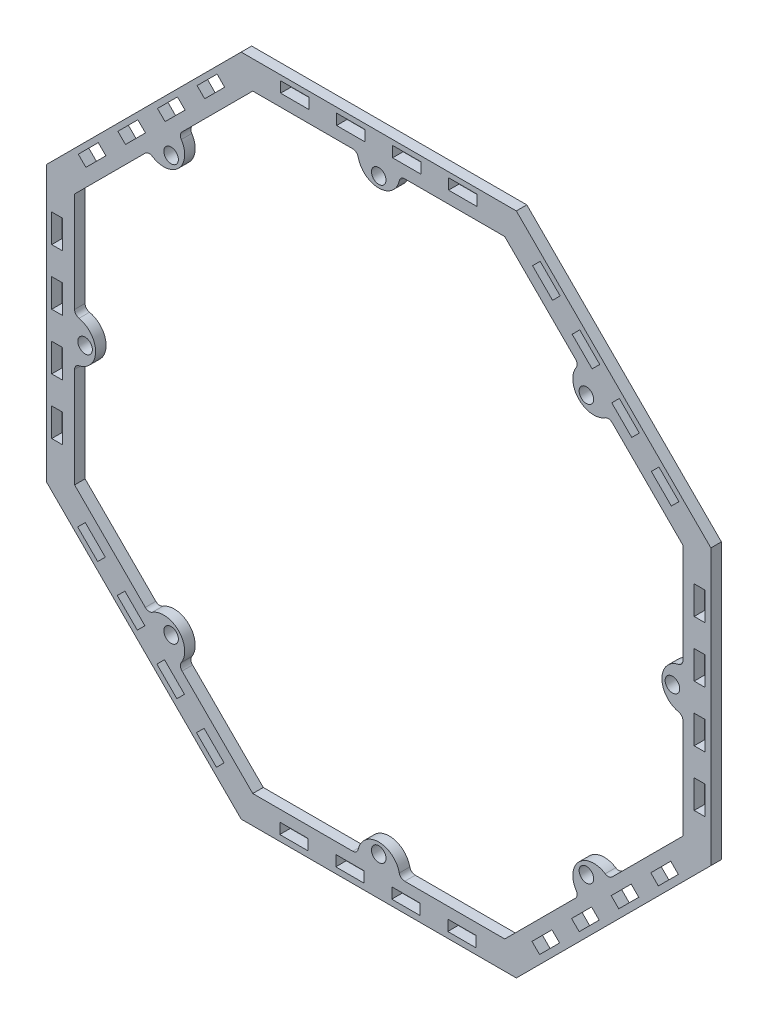
SolidWorks part; units mm, degrees
material "6061-T6 (SS)"
ref_plane "Front Plane" through (0, 0, 0) normal (0, 0, 1) x (1, 0, 0)
ref_plane "Top Plane" through (0, 0, 0) normal (0, 1, 0) x (1, 0, 0)
ref_plane "Right Plane" through (0, 0, 0) normal (1, 0, 0) x (0, 0, -1)
sketch "Sketch1" plane through (0, 0, 0) normal (0, 0, 1) x (1, 0, 0)
  line L0 (-150.6696, -62.417) -> (-62.404, -150.675)
  line L1 (-137.9698, -57.1559) -> (-57.1441, -137.9748)
  line L2 (-57.1441, -137.9748) -> (57.1559, -137.9698)
  line L3 (57.1559, -137.9698) -> (137.9748, -57.1441)
  line L4 (137.9748, -57.1441) -> (137.9698, 57.1559)
  line L5 (137.9698, 57.1559) -> (57.1441, 137.9748)
  line L6 (57.1441, 137.9748) -> (-57.1559, 137.9698)
  line L7 (-57.1559, 137.9698) -> (-137.9748, 57.1441)
  line L8 (-137.9748, 57.1441) -> (-137.9698, -57.1559)
  line L9 (-62.404, -150.675) -> (62.417, -150.6696)
  line L10 (62.417, -150.6696) -> (150.675, -62.404)
  line L11 (150.675, -62.404) -> (150.6696, 62.417)
  line L12 (150.6696, 62.417) -> (62.404, 150.675)
  line L13 (62.404, 150.675) -> (-62.417, 150.6696)
  line L14 (-62.417, 150.6696) -> (-150.675, 62.404)
  line L15 (-150.675, 62.404) -> (-150.6696, -62.417)
  circle A0 centre (0, 0) radius 137.9723 construction
  circle A1 centre (0, 0) radius 150.6723 construction
  dimension "D2" = 12.7
  dimension "D1" = 114.3
extrude "Boss-Extrude1" add sketch "Sketch1" along normal blind 4.7625
sketch "Sketch2" plane through (0, 0, 4.7625) normal (0, 0, 1) x (1, 0, 0)
  line L0 (57.1441, 137.9748) -> (-57.1559, 137.9698) construction
  line L1 (-57.1559, 137.9698) -> (-137.9748, 57.1441) construction
  line L2 (-104.3003, 90.8215) -> (-90.8305, 104.2924)
  line L3 (106.5368, 106.546) -> (97.5569, 97.5654) construction
  line L4 (-0.0059, 137.9723) -> (0.0059, -137.9723) construction
  line L5 (-57.1441, -137.9748) -> (57.1559, -137.9698) construction
  line L6 (-150.6723, -0.0065) -> (150.6723, 0.0065) construction
  line L7 (-150.675, 62.404) -> (-150.6696, -62.417) construction
  line L8 (150.675, -62.404) -> (150.6696, 62.417) construction
  line L9 (-106.546, 106.5368) -> (-97.5654, 97.5569) construction
  line L10 (-62.417, 150.6696) -> (-150.675, 62.404) construction
  line L11 (104.2924, 90.8305) -> (90.8215, 104.3003)
  line L12 (-106.5368, -106.546) -> (-97.5569, -97.5654) construction
  line L13 (106.546, -106.5368) -> (97.5654, -97.5569) construction
  line L14 (104.3003, -90.8215) -> (90.8305, -104.2924)
  line L15 (-104.2924, -90.8305) -> (-90.8215, -104.3003)
  line L16 (-97.5654, 97.5569) -> (-90.8299, 90.822) construction
  line L17 (97.5569, 97.5654) -> (90.822, 90.8299) construction
  line L18 (-97.5569, -97.5654) -> (-90.822, -90.8299) construction
  line L19 (97.5654, -97.5569) -> (90.8299, -90.822) construction
  line L20 (-137.9748, 57.1441) -> (-137.9698, -57.1559) construction
  line L21 (-0.0059, 137.9723) -> (-0.0055, 128.4473) construction
  line L22 (-128.4473, -0.0055) -> (-137.9723, -0.0059) construction
  line L23 (-137.9727, 9.5191) -> (-137.9719, -9.5309)
  line L24 (137.9719, 9.5309) -> (137.9727, -9.5191)
  line L25 (-0.0059, 137.9723) -> (-0.0055, 128.4473) construction
  line L26 (-9.5309, 137.9719) -> (9.5191, 137.9727)
  line L27 (0.0059, -137.9723) -> (0.0055, -128.4473) construction
  line L28 (0.0059, -137.9723) -> (0.0055, -128.4473) construction
  line L29 (-9.5191, -137.9727) -> (9.5309, -137.9719)
  arc A0 (-90.8305, 104.2924) -> (-104.3003, 90.8215) centre (-97.5654, 97.5569) cw
  arc A1 (90.8215, 104.3003) -> (104.2924, 90.8305) centre (97.5569, 97.5654) ccw
  arc A2 (90.8305, -104.2924) -> (104.3003, -90.8215) centre (97.5654, -97.5569) cw
  arc A3 (-90.8215, -104.3003) -> (-104.2924, -90.8305) centre (-97.5569, -97.5654) ccw
  circle A4 centre (-94.1976, 94.1895) radius 3.302
  circle A5 centre (94.1895, 94.1976) radius 3.302
  circle A6 centre (-94.1895, -94.1976) radius 3.302
  circle A7 centre (94.1976, -94.1895) radius 3.302
  arc A8 (-137.9727, 9.5191) -> (-137.9719, -9.5309) centre (-137.9723, -0.0059) cw
  circle A9 centre (133.2098, 0.0057) radius 3.302
  circle A10 centre (-133.2098, -0.0057) radius 3.302
  arc A11 (137.9719, 9.5309) -> (137.9727, -9.5191) centre (137.9723, 0.0059) ccw
  arc A12 (-9.5309, 137.9719) -> (9.5191, 137.9727) centre (-0.0059, 137.9723) ccw
  circle A13 centre (-0.0057, 133.2094) radius 3.302
  circle A14 centre (0.0057, -133.2094) radius 3.302
  arc A15 (-9.5191, -137.9727) -> (9.5309, -137.9719) centre (0.0059, -137.9723) cw
  dimension "D1" = 9.525
  dimension "D2" = 6.604
  dimension "D3" = 9.525
  dimension "D4" = 9.525
  dimension "D5" = 6.604
  dimension "D7" = 6.604
  dimension "D6" = 4.7625
  dimension "D8" = 4.7625
extrude "Boss-Extrude2" add sketch "Sketch2" against normal blind 4.7625
sketch "Sketch3" plane through (0, 0, 4.7625) normal (0, 0, 1) x (1, 0, 0)
  line L0 (-57.1559, 137.9698) -> (-57.1559, 150.6698) construction
  line L1 (62.404, 150.675) -> (-62.417, 150.6696) construction
  line L2 (57.1441, 137.9748) -> (57.1441, 150.6748) construction
  line L3 (-57.1559, 145.9073) -> (57.1441, 145.9123) construction
  line L4 (33.3316, 137.9737) -> (-33.3316, -137.9737) construction
  line L5 (-31.6924, 148.3466) -> (-44.5194, 148.3466)
  line L6 (-31.6924, 148.3466) -> (-31.6924, 143.4698)
  line L7 (-31.6924, 143.4698) -> (-44.5194, 143.4698)
  line L8 (-44.5194, 148.3466) -> (-44.5194, 143.4698)
  line L9 (-31.6924, 148.3466) -> (-44.5194, 143.4698) construction
  line L10 (-31.6924, 143.4698) -> (-44.5194, 148.3466) construction
  line L11 (96.8055, 105.8176) -> (87.7354, 114.8877)
  line L12 (100.2539, 109.266) -> (96.8055, 105.8176)
  line L13 (100.2539, 109.266) -> (91.1838, 118.3361)
  line L14 (91.1838, 118.3361) -> (87.7354, 114.8877)
  line L15 (96.8055, 105.8176) -> (91.1838, 118.3361) construction
  line L16 (100.2539, 109.266) -> (87.7354, 114.8877) construction
  line L17 (19.1076, 148.3488) -> (6.2806, 148.3488)
  line L18 (19.1076, 148.3488) -> (19.1076, 143.472)
  line L19 (19.1076, 143.472) -> (6.2806, 143.472)
  line L20 (6.2806, 148.3488) -> (6.2806, 143.472)
  line L21 (19.1076, 148.3488) -> (6.2806, 143.472) construction
  line L22 (19.1076, 143.472) -> (6.2806, 148.3488) construction
  line L23 (136.1765, 73.3466) -> (127.1064, 82.4166)
  line L24 (136.1765, 73.3466) -> (132.728, 69.8981)
  line L25 (132.728, 69.8981) -> (123.658, 78.9682)
  line L26 (127.1064, 82.4166) -> (123.658, 78.9682)
  line L27 (136.1765, 73.3466) -> (123.658, 78.9682) construction
  line L28 (132.728, 69.8981) -> (127.1064, 82.4166) construction
  line L29 (57.1441, 137.9748) -> (9.5191, 137.9727) construction
  line L30 (-57.1441, -137.9748) -> (-9.5191, -137.9727) construction
  line L31 (-137.9737, 33.3316) -> (137.9737, -33.3316) construction
  line L32 (-137.9748, 57.1441) -> (-137.9727, 9.5191) construction
  line L33 (137.9748, -57.1441) -> (137.9727, -9.5191) construction
  line L34 (106.5368, 106.546) -> (-106.5368, -106.546) construction
  line L35 (150.6696, 62.417) -> (62.404, 150.675) construction
  line L36 (-150.6696, -62.417) -> (-62.404, -150.675) construction
  line L37 (-106.546, 106.5368) -> (106.546, -106.5368) construction
  line L38 (-62.417, 150.6696) -> (-150.675, 62.404) construction
  line L39 (62.417, -150.6696) -> (150.675, -62.404) construction
  line L40 (82.2926, 127.2258) -> (73.2225, 136.2958)
  line L41 (82.2926, 127.2258) -> (78.8442, 123.7773)
  line L42 (82.2926, 127.2258) -> (69.7741, 132.8474) construction
  line L43 (78.8442, 123.7773) -> (73.2225, 136.2958) construction
  line L44 (73.2225, 136.2958) -> (69.7741, 132.8474)
  line L45 (78.8442, 123.7773) -> (69.7741, 132.8474)
  line L46 (114.7668, 87.8579) -> (105.6967, 96.9279)
  line L47 (118.2152, 91.3063) -> (114.7668, 87.8579)
  line L48 (118.2152, 91.3063) -> (109.1451, 100.3764)
  line L49 (109.1451, 100.3764) -> (105.6967, 96.9279)
  line L50 (118.2152, 91.3063) -> (105.6967, 96.9279) construction
  line L51 (114.7668, 87.8579) -> (109.1451, 100.3764) construction
  line L52 (143.0818, 6.2915) -> (143.0818, 19.1185)
  line L53 (147.9586, 6.2915) -> (143.0818, 6.2915)
  line L54 (147.9586, 6.2915) -> (147.9586, 19.1185)
  line L55 (147.9586, 19.1185) -> (143.0818, 19.1185)
  line L56 (143.0818, 6.2915) -> (147.9586, 19.1185) construction
  line L57 (147.9586, 6.2915) -> (143.0818, 19.1185) construction
  line L58 (147.9608, -44.5085) -> (147.9608, -31.6815)
  line L59 (147.9608, -44.5085) -> (143.084, -44.5085)
  line L60 (143.084, -44.5085) -> (143.084, -31.6815)
  line L61 (147.9608, -31.6815) -> (143.084, -31.6815)
  line L62 (147.9608, -44.5085) -> (143.084, -31.6815) construction
  line L63 (143.084, -44.5085) -> (147.9608, -31.6815) construction
  line L64 (147.9575, 31.6915) -> (147.9575, 44.5185)
  line L65 (147.9575, 31.6915) -> (143.0807, 31.6915)
  line L66 (147.9575, 31.6915) -> (143.0807, 44.5185) construction
  line L67 (143.0807, 31.6915) -> (147.9575, 44.5185) construction
  line L68 (147.9575, 44.5185) -> (143.0807, 44.5185)
  line L69 (143.0807, 31.6915) -> (143.0807, 44.5185)
  line L70 (143.0829, -19.1085) -> (143.0829, -6.2815)
  line L71 (147.9597, -19.1085) -> (143.0829, -19.1085)
  line L72 (147.9597, -19.1085) -> (147.9597, -6.2815)
  line L73 (147.9597, -6.2815) -> (143.0829, -6.2815)
  line L74 (147.9597, -19.1085) -> (143.0829, -6.2815) construction
  line L75 (143.0829, -19.1085) -> (147.9597, -6.2815) construction
  line L76 (105.4286, -96.8064) -> (114.4986, -87.7363)
  line L77 (108.877, -100.2548) -> (105.4286, -96.8064)
  line L78 (108.877, -100.2548) -> (117.9471, -91.1848)
  line L79 (117.9471, -91.1848) -> (114.4986, -87.7363)
  line L80 (105.4286, -96.8064) -> (117.9471, -91.1848) construction
  line L81 (108.877, -100.2548) -> (114.4986, -87.7363) construction
  line L82 (72.9575, -136.1774) -> (82.0276, -127.1073)
  line L83 (72.9575, -136.1774) -> (69.5091, -132.729)
  line L84 (69.5091, -132.729) -> (78.5792, -123.6589)
  line L85 (82.0276, -127.1073) -> (78.5792, -123.6589)
  line L86 (72.9575, -136.1774) -> (78.5792, -123.6589) construction
  line L87 (69.5091, -132.729) -> (82.0276, -127.1073) construction
  line L88 (126.8367, -82.2935) -> (135.9068, -73.2235)
  line L89 (126.8367, -82.2935) -> (123.3883, -78.8451)
  line L90 (126.8367, -82.2935) -> (132.4584, -69.7751) construction
  line L91 (123.3883, -78.8451) -> (135.9068, -73.2235) construction
  line L92 (135.9068, -73.2235) -> (132.4584, -69.7751)
  line L93 (123.3883, -78.8451) -> (132.4584, -69.7751)
  line L94 (87.4689, -114.7677) -> (96.5389, -105.6976)
  line L95 (90.9173, -118.2161) -> (87.4689, -114.7677)
  line L96 (90.9173, -118.2161) -> (99.9873, -109.146)
  line L97 (99.9873, -109.146) -> (96.5389, -105.6976)
  line L98 (90.9173, -118.2161) -> (96.5389, -105.6976) construction
  line L99 (87.4689, -114.7677) -> (99.9873, -109.146) construction
  line L100 (5.9025, -143.0828) -> (18.7295, -143.0828)
  line L101 (5.9025, -147.9596) -> (5.9025, -143.0828)
  line L102 (5.9025, -147.9596) -> (18.7295, -147.9596)
  line L103 (18.7295, -147.9596) -> (18.7295, -143.0828)
  line L104 (5.9025, -143.0828) -> (18.7295, -147.9596) construction
  line L105 (5.9025, -147.9596) -> (18.7295, -143.0828) construction
  line L106 (-44.8975, -147.9618) -> (-32.0705, -147.9618)
  line L107 (-44.8975, -147.9618) -> (-44.8975, -143.085)
  line L108 (-44.8975, -143.085) -> (-32.0705, -143.085)
  line L109 (-32.0705, -147.9618) -> (-32.0705, -143.085)
  line L110 (-44.8975, -147.9618) -> (-32.0705, -143.085) construction
  line L111 (-44.8975, -143.085) -> (-32.0705, -147.9618) construction
  line L112 (31.3025, -147.9585) -> (44.1295, -147.9585)
  line L113 (44.5076, 148.3498) -> (31.6806, 148.3498)
  line L114 (44.5076, 148.3498) -> (44.5076, 143.473)
  line L115 (44.5076, 143.473) -> (31.6806, 143.473)
  line L116 (31.6806, 148.3498) -> (31.6806, 143.473)
  line L117 (44.5076, 148.3498) -> (31.6806, 143.473) construction
  line L118 (44.5076, 143.473) -> (31.6806, 148.3498) construction
  line L119 (-6.2924, 148.3477) -> (-19.1194, 148.3477)
  line L120 (-6.2924, 148.3477) -> (-6.2924, 143.4709)
  line L121 (-6.2924, 143.4709) -> (-19.1194, 143.4709)
  line L122 (-19.1194, 148.3477) -> (-19.1194, 143.4709)
  line L123 (-6.2924, 148.3477) -> (-19.1194, 143.4709) construction
  line L124 (-6.2924, 143.4709) -> (-19.1194, 148.3477) construction
  line L125 (31.3025, -147.9585) -> (31.3025, -143.0817)
  line L126 (31.3025, -147.9585) -> (44.1295, -143.0817) construction
  line L127 (31.3025, -143.0817) -> (44.1295, -147.9585) construction
  line L128 (44.1295, -147.9585) -> (44.1295, -143.0817)
  line L129 (31.3025, -143.0817) -> (44.1295, -143.0817)
  line L130 (-19.4975, -143.0839) -> (-6.6705, -143.0839)
  line L131 (-19.4975, -147.9607) -> (-19.4975, -143.0839)
  line L132 (-19.4975, -147.9607) -> (-6.6705, -147.9607)
  line L133 (-6.6705, -147.9607) -> (-6.6705, -143.0839)
  line L134 (-19.4975, -147.9607) -> (-6.6705, -143.0839) construction
  line L135 (-19.4975, -143.0839) -> (-6.6705, -147.9607) construction
  line L136 (-97.1954, -105.4295) -> (-88.1254, -114.4996)
  line L137 (-100.6438, -108.8779) -> (-97.1954, -105.4295)
  line L138 (-100.6438, -108.8779) -> (-91.5738, -117.948)
  line L139 (-91.5738, -117.948) -> (-88.1254, -114.4996)
  line L140 (-97.1954, -105.4295) -> (-91.5738, -117.948) construction
  line L141 (-100.6438, -108.8779) -> (-88.1254, -114.4996) construction
  line L142 (-136.5664, -72.9585) -> (-127.4964, -82.0285)
  line L143 (-136.5664, -72.9585) -> (-133.118, -69.51)
  line L144 (-133.118, -69.51) -> (-124.0479, -78.5801)
  line L145 (-127.4964, -82.0285) -> (-124.0479, -78.5801)
  line L146 (-136.5664, -72.9585) -> (-124.0479, -78.5801) construction
  line L147 (-133.118, -69.51) -> (-127.4964, -82.0285) construction
  line L148 (-82.6826, -126.8377) -> (-73.6125, -135.9077)
  line L149 (-82.6826, -126.8377) -> (-79.2341, -123.3893)
  line L150 (-82.6826, -126.8377) -> (-70.1641, -132.4593) construction
  line L151 (-79.2341, -123.3893) -> (-73.6125, -135.9077) construction
  line L152 (-73.6125, -135.9077) -> (-70.1641, -132.4593)
  line L153 (-79.2341, -123.3893) -> (-70.1641, -132.4593)
  line L154 (-115.1567, -87.4698) -> (-106.0867, -96.5398)
  line L155 (-118.6051, -90.9182) -> (-115.1567, -87.4698)
  line L156 (-118.6051, -90.9182) -> (-109.5351, -99.9883)
  line L157 (-109.5351, -99.9883) -> (-106.0867, -96.5398)
  line L158 (-118.6051, -90.9182) -> (-106.0867, -96.5398) construction
  line L159 (-115.1567, -87.4698) -> (-109.5351, -99.9883) construction
  line L160 (-143.4718, -5.9034) -> (-143.4718, -18.7304)
  line L161 (-148.3486, -5.9034) -> (-143.4718, -5.9034)
  line L162 (-148.3486, -5.9034) -> (-148.3486, -18.7304)
  line L163 (-148.3486, -18.7304) -> (-143.4718, -18.7304)
  line L164 (-143.4718, -5.9034) -> (-148.3486, -18.7304) construction
  line L165 (-148.3486, -5.9034) -> (-143.4718, -18.7304) construction
  line L166 (-148.3508, 44.8966) -> (-148.3508, 32.0696)
  line L167 (-148.3508, 44.8966) -> (-143.474, 44.8966)
  line L168 (-143.474, 44.8966) -> (-143.474, 32.0696)
  line L169 (-148.3508, 32.0696) -> (-143.474, 32.0696)
  line L170 (-148.3508, 44.8966) -> (-143.474, 32.0696) construction
  line L171 (-143.474, 44.8966) -> (-148.3508, 32.0696) construction
  line L172 (-148.3475, -31.3034) -> (-148.3475, -44.1304)
  line L173 (-148.3475, -31.3034) -> (-143.4707, -31.3034)
  line L174 (-148.3475, -31.3034) -> (-143.4707, -44.1304) construction
  line L175 (-143.4707, -31.3034) -> (-148.3475, -44.1304) construction
  line L176 (-148.3475, -44.1304) -> (-143.4707, -44.1304)
  line L177 (-143.4707, -31.3034) -> (-143.4707, -44.1304)
  line L178 (-143.4729, 19.4966) -> (-143.4729, 6.6696)
  line L179 (-148.3497, 19.4966) -> (-143.4729, 19.4966)
  line L180 (-148.3497, 19.4966) -> (-148.3497, 6.6696)
  line L181 (-148.3497, 6.6696) -> (-143.4729, 6.6696)
  line L182 (-148.3497, 19.4966) -> (-143.4729, 6.6696) construction
  line L183 (-143.4729, 19.4966) -> (-148.3497, 6.6696) construction
  line L184 (-105.8185, 97.1945) -> (-114.8886, 88.1244)
  line L185 (-109.267, 100.6429) -> (-105.8185, 97.1945)
  line L186 (-109.267, 100.6429) -> (-118.337, 91.5728)
  line L187 (-118.337, 91.5728) -> (-114.8886, 88.1244)
  line L188 (-105.8185, 97.1945) -> (-118.337, 91.5728) construction
  line L189 (-109.267, 100.6429) -> (-114.8886, 88.1244) construction
  line L190 (-73.3475, 136.5655) -> (-82.4175, 127.4954)
  line L191 (-73.3475, 136.5655) -> (-69.8991, 133.1171)
  line L192 (-69.8991, 133.1171) -> (-78.9691, 124.047)
  line L193 (-82.4175, 127.4954) -> (-78.9691, 124.047)
  line L194 (-73.3475, 136.5655) -> (-78.9691, 124.047) construction
  line L195 (-69.8991, 133.1171) -> (-82.4175, 127.4954) construction
  line L196 (-127.2267, 82.6816) -> (-136.2968, 73.6116)
  line L197 (-127.2267, 82.6816) -> (-123.7783, 79.2332)
  line L198 (-127.2267, 82.6816) -> (-132.8483, 70.1631) construction
  line L199 (-123.7783, 79.2332) -> (-136.2968, 73.6116) construction
  line L200 (-136.2968, 73.6116) -> (-132.8483, 70.1631)
  line L201 (-123.7783, 79.2332) -> (-132.8483, 70.1631)
  line L202 (-87.8588, 115.1558) -> (-96.9289, 106.0857)
  line L203 (-91.3072, 118.6042) -> (-87.8588, 115.1558)
  line L204 (-91.3072, 118.6042) -> (-100.3773, 109.5341)
  line L205 (-100.3773, 109.5341) -> (-96.9289, 106.0857)
  line L206 (-91.3072, 118.6042) -> (-96.9289, 106.0857) construction
  line L207 (-87.8588, 115.1558) -> (-100.3773, 109.5341) construction
  point P10 (-38.1059, 145.9082)
  point P15 (38.0941, 145.9114)
  point P20 (12.6941, 145.9104)
  point P105 (-12.7059, 145.9093)
  dimension "D1" = 4.8768
  dimension "D2" = 12.827
  dimension "D3" = 19.05
  dimension "D4" = 25.4
  dimension "D5" = 7.9375
  dimension "D6" = 12.827
  dimension "D7" = 4.8768
  dimension "D8" = 12.827
  dimension "D9" = 12.827
  dimension "D10" = 4.8768
  dimension "D11" = 4.8768
  dimension "D12" = 25.4
  dimension "D13" = 25.4
  dimension "D15" = 7.9375
  dimension "D16" = 114.3
  dimension "D14" = 8
extrude "Panel Slots" cut sketch "Sketch3" against normal through all
sketch "Sketch4" plane through (0, 0, 4.7625) normal (0, 0, 1) x (1, 0, 0)
  line L0 (-137.9748, 57.1441) -> (-137.9727, 9.5191) construction
  circle A0 centre (0, 0) radius 137.9723 construction
sketch "Sketch5" plane through (0, 0, 4.7625) normal (0, 0, 1) x (1, 0, 0)
  line L0 (57.1441, 137.9748) -> (105.7398, 255.3096) construction
  line L1 (63.0108, 135.545) -> (111.6065, 252.8798)
  line L2 (51.2773, 140.4046) -> (99.8731, 257.7393)
  line L3 (51.2773, 140.4046) -> (63.0108, 135.545)
  line L4 (-51.2773, 140.4046) -> (-63.0108, 135.545)
  line L5 (0, 210.8054) -> (0, -211.0379) construction
  line L6 (236.5526, 0) -> (-245.9763, 0) construction
  line L7 (-63.0108, 135.545) -> (-111.6065, 252.8798)
  line L8 (-51.2773, 140.4046) -> (-99.8731, 257.7393)
  line L9 (-51.2773, -140.4046) -> (-63.0108, -135.545)
  line L10 (-63.0108, -135.545) -> (-111.6065, -252.8798)
  line L11 (-51.2773, -140.4046) -> (-99.8731, -257.7393)
  line L12 (51.2773, -140.4046) -> (63.0108, -135.545)
  line L13 (51.2773, -140.4046) -> (99.8731, -257.7393)
  line L14 (63.0108, -135.545) -> (111.6065, -252.8798)
  arc A0 (99.8731, 257.7393) -> (111.6065, 252.8798) centre (105.7398, 255.3096) cw
  arc A1 (-99.8731, 257.7393) -> (-111.6065, 252.8798) centre (-105.7398, 255.3096) ccw
  arc A2 (-99.8731, -257.7393) -> (-111.6065, -252.8798) centre (-105.7398, -255.3096) cw
  arc A3 (99.8731, -257.7393) -> (111.6065, -252.8798) centre (105.7398, -255.3096) ccw
  dimension "D4" = 6.35
  dimension "D1" = 127
  dimension "D2" = 6.35
  dimension "D3" = 6.35
extrude "Boss-Extrude5" [suppressed] add sketch "Sketch5" against normal blind 4.7625
sketch "Sketch6" plane through (0, 0, 4.7625) normal (0, 0, 1) x (1, 0, 0)
  line L0 (90.822, 90.8299) -> (216.5402, 216.5589) construction
  line L1 (106.5368, 106.546) -> (196.3355, 196.3524) construction
  line L2 (150.6696, 62.417) -> (62.404, 150.675) construction
  line L3 (90.822, 90.8299) -> (216.5402, 216.5589) construction
  line L4 (124.4981, 88.5863) -> (234.5015, 198.5991)
  line L5 (106.5368, 106.546) -> (196.3355, 196.3524) construction
  line L6 (88.5755, 124.5057) -> (198.5789, 234.5186)
  line L7 (150.6697, 60.8762) -> (261.4434, 171.6595)
  line L8 (60.8633, 150.6749) -> (171.637, 261.4582)
  line L9 (150.6697, 60.8762) -> (150.6696, 62.417)
  line L10 (-106.546, 106.5368) -> (106.546, -106.5368) construction
  line L11 (-62.417, 150.6696) -> (-150.675, 62.404) construction
  line L12 (62.417, -150.6696) -> (150.675, -62.404) construction
  line L13 (-150.6723, -0.0065) -> (150.6723, 0.0065) construction
  line L14 (-150.675, 62.404) -> (-150.6696, -62.417) construction
  line L15 (150.675, -62.404) -> (150.6696, 62.417) construction
  line L16 (60.8633, 150.6749) -> (62.404, 150.675)
  line L17 (62.404, 150.675) -> (-62.417, 150.6696) construction
  line L18 (62.404, 150.675) -> (88.5755, 124.5057)
  line L19 (150.6696, 62.417) -> (62.404, 150.675) construction
  line L20 (150.6696, 62.417) -> (124.4981, 88.5863)
  line L22 (45.9188, 135.7292) -> (171.637, 261.4582) construction
  line L23 (72.8608, 108.7896) -> (198.5789, 234.5186) construction
  line L24 (108.7833, 72.8701) -> (234.5015, 198.5991) construction
  line L25 (135.7253, 45.9305) -> (261.4434, 171.6595) construction
  arc A0 (90.8215, 104.3003) -> (104.2924, 90.8305) centre (97.5569, 97.5654) ccw construction
  arc A1 (198.5789, 234.5186) -> (234.5015, 198.5991) centre (216.5402, 216.5589) cw
  arc A2 (171.637, 261.4582) -> (261.4434, 171.6595) centre (216.5402, 216.5589) cw
  circle A3 centre (153.6811, 153.6944) radius 50.8 construction
  dimension "D6" = 63.5
  dimension "D7" = 25.4
  dimension "D8" = 101.6
  dimension "D9" = 88.9
  dimension "D10" = 63.5
  dimension "D1" = 127
  dimension "D2" = 177.8
  dimension "D3" = 25.4
  dimension "D4" = 25.4
  dimension "D5" = 63.5
extrude "Boss-Extrude6" [suppressed] add sketch "Sketch6" against normal blind 4.7625
sketch "Sketch7" [suppressed] plane through (0, 0, 4.7625) normal (0, 0, 1) x (1, 0, 0)
  line L0 (96.7827, 186.5975) -> (186.5892, 96.7988) construction
  line L3 (171.637, 261.4582) -> (60.8633, 150.6749) construction
  line L4 (150.6697, 60.8762) -> (261.4434, 171.6595) construction
  circle A0 centre (141.6859, 141.6982) radius 49.2125
  dimension "D1" = 50.8
  dimension "D2" = 98.425
extrude "Cut-Extrude1" [suppressed] cut sketch "Sketch7" against normal blind 4.7625
fillet "Fillet1" [suppressed] radius 2.54
sketch "Sketch9" plane through (0, 0, 4.7625) normal (0, 0, 1) x (1, 0, 0)
  line L0 (90.822, 90.8299) -> (207.5603, 207.5782) construction
  line L1 (62.404, 150.675) -> (158.4549, 220.5897)
  line L2 (220.5761, 158.474) -> (150.6696, 62.417)
  line L3 (158.4549, 220.5897) -> (220.5761, 158.474) construction
  line L4 (150.6696, 62.417) -> (62.404, 150.675) construction
  line L5 (62.404, 150.675) -> (150.6696, 62.417)
  line L6 (-150.6723, -0.0065) -> (150.6723, 0.0065) construction
  line L7 (-150.675, 62.404) -> (-150.6696, -62.417) construction
  line L8 (150.675, -62.404) -> (150.6696, 62.417) construction
  line L9 (158.474, -220.5761) -> (220.5897, -158.4549) construction
  line L10 (90.8299, -90.822) -> (207.5782, -207.5603) construction
  line L11 (62.417, -150.6696) -> (150.675, -62.404)
  line L12 (220.5897, -158.4549) -> (150.675, -62.404)
  line L13 (62.417, -150.6696) -> (158.474, -220.5761)
  line L14 (0, 137.9723) -> (0, -137.9723) construction
  line L15 (-106.546, 106.5368) -> (106.546, -106.5368) construction
  line L16 (-62.417, 150.6696) -> (-150.675, 62.404) construction
  line L17 (-220.5761, -158.474) -> (-158.4549, -220.5897) construction
  line L18 (-90.822, -90.8299) -> (-207.5603, -207.5782) construction
  line L19 (-150.6696, -62.417) -> (-62.404, -150.675)
  line L20 (-158.4549, -220.5897) -> (-62.404, -150.675)
  line L21 (-150.6696, -62.417) -> (-220.5761, -158.474)
  line L22 (-90.8299, 90.822) -> (-207.5782, 207.5603) construction
  line L23 (-220.5897, 158.4549) -> (-158.474, 220.5761) construction
  line L24 (-150.675, 62.404) -> (-220.5897, 158.4549)
  line L25 (-158.474, 220.5761) -> (-62.417, 150.6696)
  line L26 (-150.675, 62.404) -> (-62.417, 150.6696)
  arc A0 (90.8215, 104.3003) -> (104.2924, 90.8305) centre (97.5569, 97.5654) ccw construction
  arc A1 (220.5761, 158.474) -> (158.4549, 220.5897) centre (207.5603, 207.5782) ccw
  arc A2 (220.5897, -158.4549) -> (158.474, -220.5761) centre (207.5782, -207.5603) cw
  circle A3 centre (0, 0) radius 137.9723 construction
  arc A4 (-158.4549, -220.5897) -> (-220.5761, -158.474) centre (-207.5603, -207.5782) cw
  arc A5 (-158.474, 220.5761) -> (-220.5897, 158.4549) centre (-207.5782, 207.5603) ccw
  dimension "D2" = 50.8
  dimension "D1" = 165.1
extrude "Boss-Extrude7" [suppressed] add sketch "Sketch9" against normal blind 4.7625
sketch "Sketch10" [suppressed] plane through (0, 0, 4.7625) normal (0, 0, 1) x (1, 0, 0)
  line L0 (90.822, 90.8299) -> (243.4798, 243.5008) construction
  line L1 (-0.0065, 150.6723) -> (0.0065, -150.6723) construction
  line L2 (62.404, 150.675) -> (-62.417, 150.6696) construction
  line L3 (-62.404, -150.675) -> (62.417, -150.6696) construction
  line L4 (-90.8299, 90.822) -> (90.8299, -90.822) construction
  line L5 (-150.6723, -0.0065) -> (150.6723, 0.0065) construction
  line L6 (-150.675, 62.404) -> (-150.6696, -62.417) construction
  line L7 (150.675, -62.404) -> (150.6696, 62.417) construction
  line L8 (188.4095, 240.5154) -> (240.4991, 188.4302) construction
  line L9 (90.8215, 104.3003) -> (57.1441, 137.9748) construction
  line L10 (-240.4991, -188.4302) -> (-188.4095, -240.5154) construction
  line L11 (-90.822, -90.8299) -> (-243.4798, -243.5008) construction
  line L12 (188.4302, -240.4991) -> (240.5154, -188.4095) construction
  line L13 (90.8299, -90.822) -> (243.5008, -243.4798) construction
  line L14 (-188.4302, 240.4991) -> (-240.5154, 188.4095) construction
  line L15 (-90.8299, 90.822) -> (-243.5008, 243.4798) construction
  arc A0 (90.8215, 104.3003) -> (104.2924, 90.8305) centre (97.5569, 97.5654) ccw construction
  arc A1 (220.5761, 158.474) -> (158.4549, 220.5897) centre (207.5603, 207.5782) ccw construction
  circle A2 centre (140.2113, 140.2234) radius 44.45
  arc A3 (240.4991, 188.4302) -> (188.4095, 240.5154) centre (207.5603, 207.5782) ccw
  arc A4 (243.244, 186.8345) -> (186.8136, 243.2601) centre (207.5603, 207.5782) ccw
  arc A5 (237.7542, 190.0259) -> (190.0054, 237.7706) centre (207.5603, 207.5782) ccw
  arc A6 (243.244, 186.8345) -> (237.7542, 190.0259) centre (240.4991, 188.4302) cw
  arc A7 (186.8136, 243.2601) -> (190.0054, 237.7706) centre (188.4095, 240.5154) ccw
  arc A8 (-104.3003, 90.8215) -> (-90.8305, 104.2924) centre (-97.5654, 97.5569) ccw construction
  arc A9 (104.3003, -90.8215) -> (90.8305, -104.2924) centre (97.5654, -97.5569) ccw construction
  arc A10 (-243.244, -186.8345) -> (-237.7542, -190.0259) centre (-240.4991, -188.4302) cw
  arc A11 (-186.8136, -243.2601) -> (-190.0054, -237.7706) centre (-188.4095, -240.5154) ccw
  arc A12 (-190.0054, -237.7706) -> (-237.7542, -190.0259) centre (-207.5603, -207.5782) cw
  arc A13 (-186.8136, -243.2601) -> (-243.244, -186.8345) centre (-207.5603, -207.5782) cw
  arc A14 (-188.4095, -240.5154) -> (-240.4991, -188.4302) centre (-207.5603, -207.5782) cw
  circle A15 centre (-140.2113, -140.2234) radius 44.45
  arc A16 (186.8345, -243.244) -> (190.0259, -237.7542) centre (188.4302, -240.4991) cw
  arc A17 (243.2601, -186.8136) -> (237.7706, -190.0054) centre (240.5154, -188.4095) ccw
  arc A18 (237.7706, -190.0054) -> (190.0259, -237.7542) centre (207.5782, -207.5603) cw
  arc A19 (243.2601, -186.8136) -> (186.8345, -243.244) centre (207.5782, -207.5603) cw
  arc A20 (240.5154, -188.4095) -> (188.4302, -240.4991) centre (207.5782, -207.5603) cw
  circle A21 centre (140.2234, -140.2113) radius 44.45
  arc A22 (-186.8345, 243.244) -> (-190.0259, 237.7542) centre (-188.4302, 240.4991) cw
  arc A23 (-243.2601, 186.8136) -> (-237.7706, 190.0054) centre (-240.5154, 188.4095) ccw
  arc A24 (-237.7706, 190.0054) -> (-190.0259, 237.7542) centre (-207.5782, 207.5603) cw
  arc A25 (-243.2601, 186.8136) -> (-186.8345, 243.244) centre (-207.5782, 207.5603) cw
  arc A26 (-240.5154, 188.4095) -> (-188.4302, 240.4991) centre (-207.5782, 207.5603) cw
  circle A27 centre (-140.2234, 140.2113) radius 44.45
  dimension "D1" = 88.9
  dimension "D3" = 38.1
  dimension "D2" = 69.85
  dimension "D4" = 3.175
  dimension "D5" = 3.175
extrude "Cut-Extrude3" [suppressed] cut sketch "Sketch10" against normal blind 4.7625
hole_wizard "1/4 Clearance Hole1" [suppressed] positions "Sketch13" profile "Sketch12" hole size "1/4" standard "Ansi Inch"
sketch "Sketch13" [suppressed] plane through (0, 0, 4.7625) normal (0, 0, 1) x (1, 0, 0)
  line L1 (-243.5008, 243.4798) -> (-207.5782, 207.5603) construction
  line L3 (-243.4798, -243.5008) -> (-207.5603, -207.5782) construction
  line L5 (243.5008, -243.4798) -> (207.5782, -207.5603) construction
  line L6 (232.255, 232.275) -> (214.2952, 214.3137) construction
  line L8 (90.8215, 104.3003) -> (57.1441, 137.9748) construction
  arc A1 (-158.474, 220.5761) -> (-220.5897, 158.4549) centre (-207.5782, 207.5603) ccw construction
  arc A2 (-220.5761, -158.474) -> (-158.4549, -220.5897) centre (-207.5603, -207.5782) ccw construction
  arc A3 (158.474, -220.5761) -> (220.5897, -158.4549) centre (207.5782, -207.5603) ccw construction
  arc A4 (237.7542, 190.0259) -> (190.0054, 237.7706) centre (207.5603, 207.5782) ccw construction
  point P0 (214.2952, 214.3137)
  point P33 (-207.5782, 207.5603)
  point P35 (-207.5603, -207.5782)
  point P37 (207.5782, -207.5603)
  dimension "D1" = 25.4
sketch "Sketch12" plane through (214.2952, 214.3137, 4.7625) normal (1, 0, 0) x (0, -1, 0)
  line L0 (0, 0) -> (0, 27.4298)
  line L1 (0, 27.4298) -> (3.3782, 25.4)
  line L2 (3.3782, 25.4) -> (3.3782, 0)
  line L5 (3.3782, 0) -> (0, 0)
  line L10 (0, 27.4298) -> (-3.3782, 25.4) construction
  line L11 (0, -6.35) -> (0, 107.95) construction
  dimension "Hole Dia." = 6.7564
  dimension "Hole Depth" = 25.4
  dimension "Drill Angle" = 118
fillet "Fillet2" radius 2.54 16 edges at (-90.8215, -104.3003, 2.3813) (-104.2924, -90.8305, 2.3813) (9.5309, -137.9719, 2.3813) (-9.5191, -137.9727, 2.3813) (104.3003, -90.8215, 2.3813) (90.8305, -104.2924, 2.3813) (90.8215, 104.3003, 2.3813) (104.2924, 90.8305, 2.3813) (137.9719, 9.5309, 2.3813) (137.9727, -9.5191, 2.3813) (-9.5309, 137.9719, 2.3813) (9.5191, 137.9727, 2.3813) (-104.3003, 90.8215, 2.3813) (-90.8305, 104.2924, 2.3813) (-137.9719, -9.5309, 2.3813) (-137.9727, 9.5191, 2.3813)
